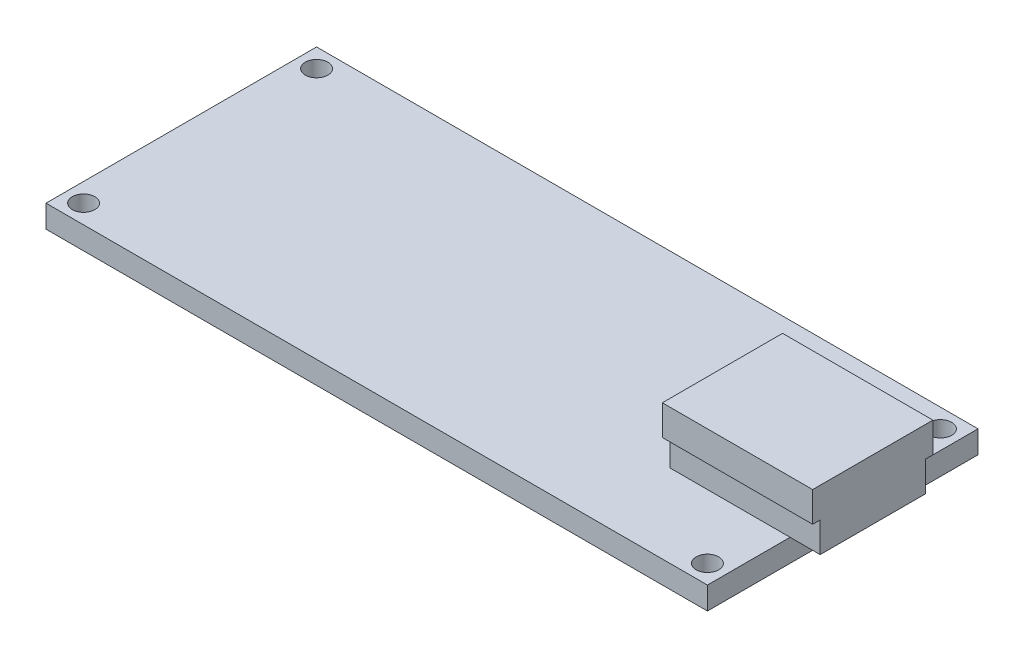
SolidWorks part; units mm, degrees
ref_plane "Piano frontale" through (0, 0, 0) normal (0, 0, 1) x (1, 0, 0)
ref_plane "Piano superiore" through (0, 0, 0) normal (0, 1, 0) x (1, 0, 0)
ref_plane "Piano destro" through (0, 0, 0) normal (1, 0, 0) x (0, 0, -1)
sketch "Schizzo1" plane through (0, 0, 0) normal (0, 1, 0) x (1, 0, 0)
  line L1 (22, -9) -> (-22, -9)
  line L2 (22, -9) -> (22, 9)
  line L3 (22, 9) -> (-22, 9)
  line L4 (-22, -9) -> (-22, 9)
  line L5 (22, -9) -> (-22, 9) construction
  line L6 (22, 9) -> (-22, -9) construction
  point P0 (0, 0)
  dimension "D1" = 18
  dimension "D2" = 44
extrude "Estrusione-Estrusione1" add sketch "Schizzo1" along normal blind 1.5
sketch "Schizzo2" plane through (0, 1.5, 0) normal (0, 1, 0) x (1, 0, 0)
  line L0 (-22, 9) -> (-22, -9) construction
  line L1 (22, 9) -> (-22, 9) construction
  line L2 (-20.75, 7.75) -> (22, 7.75) construction
  line L3 (22, -9) -> (22, 9) construction
  line L4 (20.75, 7.75) -> (20.75, -9) construction
  line L5 (-22, -9) -> (22, -9) construction
  line L6 (20.75, -7.75) -> (-22, -7.75) construction
  line L7 (-20.75, 7.75) -> (-20.75, -7.75) construction
  circle A0 centre (-20.75, 7.75) radius 0.75
  circle A1 centre (20.75, 7.75) radius 0.75
  circle A2 centre (20.75, -7.75) radius 0.75
  circle A3 centre (-20.75, -7.75) radius 0.75
  dimension "D1" = 1.5
  dimension "D5" = 1.5
  dimension "D6" = 1.5
  dimension "D8" = 1.5
  dimension "D2" = 1.25
  dimension "D3" = 1.25
  dimension "D4" = 1.25
  dimension "D7" = 1.25
extrude "Taglio-Estrusione1" cut sketch "Schizzo2" against normal blind 1.5
sketch "Schizzo3" plane through (0, 1.5, 0) normal (0, 1, 0) x (1, 0, 0)
  line L0 (22, 0) -> (-22, 0) construction
  line L1 (22, -9) -> (22, 9) construction
  line L2 (-22, 9) -> (-22, -9) construction
sketch "Schizzo4" plane through (0, 1.5, 0) normal (0, 1, 0) x (1, 0, 0)
  line L0 (22, 0) -> (-22, 0) construction
  line L1 (14, -3.5) -> (24, -3.5)
  line L2 (14, -3.5) -> (14, 3.5)
  line L3 (14, 3.5) -> (24, 3.5)
  line L4 (24, -3.5) -> (24, 3.5)
  line L5 (22, -9) -> (22, 9) construction
  dimension "D1" = 3.5
  dimension "D2" = 3.5
  dimension "D3" = 8
  dimension "D4" = 10
extrude "Estrusione-Estrusione2" add sketch "Schizzo4" along normal blind 2
sketch "Schizzo5" plane through (0, 3.5, 0) normal (0, 1, 0) x (1, 0, 0)
  line L0 (14, 3.5) -> (24, -3.5) construction
  line L1 (14, -3.5) -> (24, 3.5) construction
  line L3 (24, -4) -> (14, -4)
  line L4 (24, -4) -> (24, 4)
  line L5 (24, 4) -> (14, 4)
  line L6 (14, -4) -> (14, 4)
  line L7 (24, -4) -> (14, 4) construction
  line L8 (24, 4) -> (14, -4) construction
  point P8 (19, 0)
  dimension "D1" = 8
extrude "Estrusione-Estrusione3" add sketch "Schizzo5" along normal blind 2
